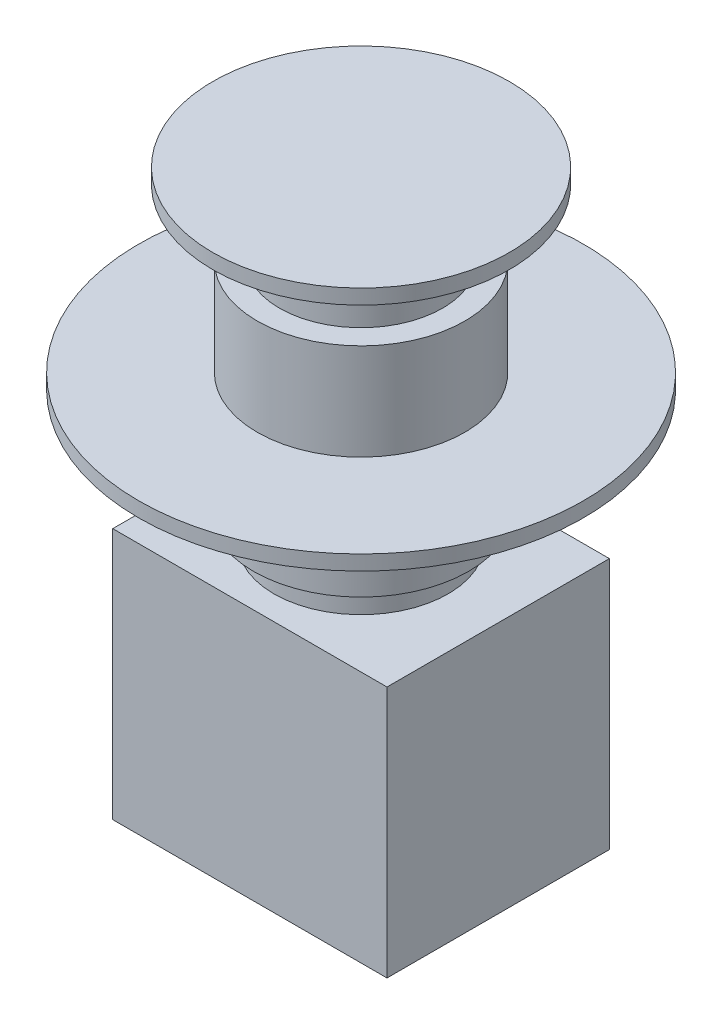
SolidWorks part; units mm, degrees
ref_plane "Plano frontal" through (0, 0, 0) normal (0, 0, 1) x (1, 0, 0)
ref_plane "Plano superior" through (0, 0, 0) normal (0, 1, 0) x (1, 0, 0)
ref_plane "Plano direito" through (0, 0, 0) normal (1, 0, 0) x (0, 0, -1)
sketch "Esboço1" plane through (0, 0, 0) normal (0, 1, 0) x (1, 0, 0)
  line L1 (18.5, -15) -> (-18.5, -15)
  line L2 (18.5, -15) -> (18.5, 15)
  line L3 (18.5, 15) -> (-18.5, 15)
  line L4 (-18.5, -15) -> (-18.5, 15)
  line L5 (18.5, -15) -> (-18.5, 15) construction
  line L6 (18.5, 15) -> (-18.5, -15) construction
  point P0 (0, 0)
  dimension "D1" = 30
  dimension "D2" = 37
extrude "Ressalto-extrusão1" add sketch "Esboço1" along normal blind 34
sketch "Esboço2" plane through (0, 34, 0) normal (0, 1, 0) x (1, 0, 0)
  circle A0 centre (0, 0) radius 11.75
  dimension "D1" = 23.5
extrude "Ressalto-extrusão2" add sketch "Esboço2" along normal blind 4
sketch "Esboço3" plane through (0, 38, 0) normal (0, 1, 0) x (1, 0, 0)
  circle A0 centre (0, 0) radius 14.5
  dimension "D1" = 29
extrude "Ressalto-extrusão3" add sketch "Esboço3" along normal blind 8
sketch "Esboço4" plane through (0, 46, 0) normal (0, 1, 0) x (1, 0, 0)
  circle A0 centre (0, 0) radius 13
  dimension "D1" = 26
extrude "Ressalto-extrusão4" add sketch "Esboço4" along normal blind 1
sketch "Esboço5" plane through (0, 47, 0) normal (0, 1, 0) x (1, 0, 0)
  circle A0 centre (0, 0) radius 11
  dimension "D1" = 22
extrude "Ressalto-extrusão5" add sketch "Esboço5" along normal blind 5
sketch "Esboço6" plane through (0, 52, 0) normal (0, 1, 0) x (1, 0, 0)
  circle A0 centre (0, 0) radius 30
  dimension "D1" = 60
extrude "Ressalto-extrusão6" add sketch "Esboço6" along normal blind 2
sketch "Esboço7" plane through (0, 54, 0) normal (0, 1, 0) x (1, 0, 0)
  circle A0 centre (0, 0) radius 14
  dimension "D1" = 28
extrude "Ressalto-extrusão7" add sketch "Esboço7" along normal blind 13
sketch "Esboço8" plane through (0, 67, 0) normal (0, 1, 0) x (1, 0, 0)
  circle A0 centre (0, 0) radius 11
  dimension "D1" = 22
extrude "Ressalto-extrusão8" add sketch "Esboço8" along normal blind 9
sketch "Esboço9" plane through (0, 76, 0) normal (0, 1, 0) x (1, 0, 0)
  circle A0 centre (0, 0) radius 20
  dimension "D1" = 40
extrude "Ressalto-extrusão9" add sketch "Esboço9" along normal blind 2
